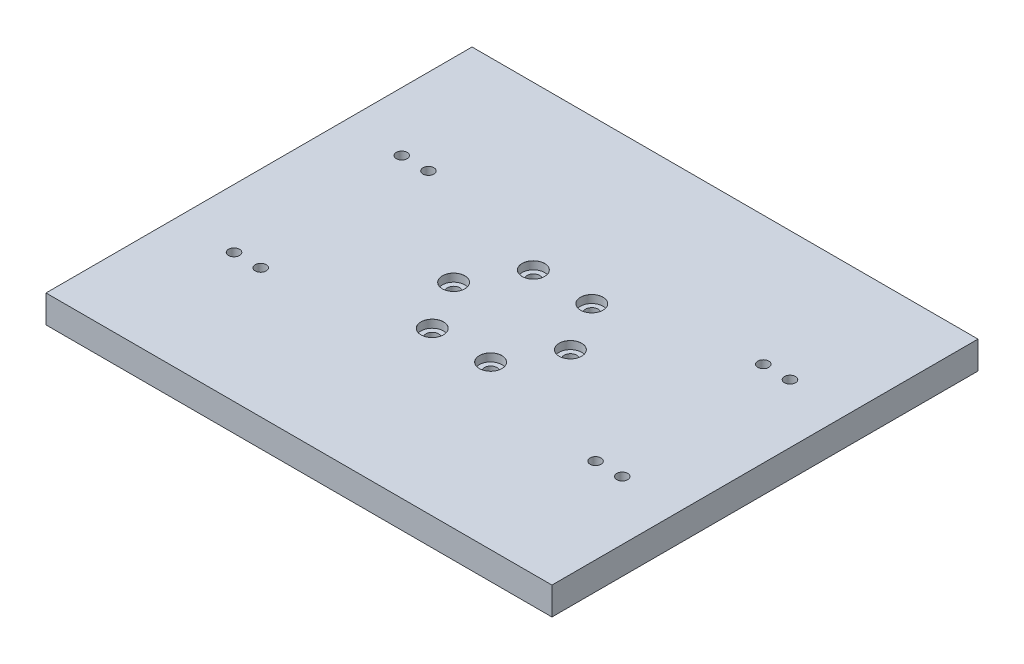
SolidWorks part; units mm, degrees
ref_plane "Front Plane" through (0, 0, 0) normal (0, 0, 1) x (1, 0, 0)
ref_plane "Top Plane" through (0, 0, 0) normal (0, 1, 0) x (1, 0, 0)
ref_plane "Right Plane" through (0, 0, 0) normal (1, 0, 0) x (0, 0, -1)
sketch "Sketch1" plane through (0, 0, 0) normal (0, 1, 0) x (1, 0, 0)
  line L1 (-241.3, -203.2) -> (241.3, -203.2)
  line L2 (-241.3, -203.2) -> (-241.3, 203.2)
  line L3 (-241.3, 203.2) -> (241.3, 203.2)
  line L4 (241.3, -203.2) -> (241.3, 203.2)
  line L5 (-241.3, -203.2) -> (241.3, 203.2) construction
  line L6 (-241.3, 203.2) -> (241.3, -203.2) construction
  point P0 (0, 0)
  dimension "D1" = 406.4
  dimension "D2" = 482.6
extrude "Boss-Extrude1" add sketch "Sketch1" along normal blind 26.416
sketch "Sketch3" plane through (0, 26.416, 0) normal (0, 1, 0) x (1, 0, 0)
  line L1 (-197.7873, -67.31) -> (-121.5873, -67.31) construction
  line L2 (-197.7873, -67.31) -> (-197.7873, -92.71) construction
  line L3 (-197.7873, -92.71) -> (-121.5873, -92.71) construction
  line L4 (-121.5873, -67.31) -> (-121.5873, -92.71) construction
  line L5 (-197.7873, -67.31) -> (-121.5873, -92.71) construction
  line L6 (-197.7873, -92.71) -> (-121.5873, -67.31) construction
  line L7 (-241.3, 203.2) -> (-241.3, -203.2) construction
  line L8 (0, 203.2) -> (0, -188.1619) construction
  line L9 (241.3, 203.2) -> (-241.3, 203.2) construction
  line L10 (-241.3, 0) -> (265.7597, 0) construction
  line L11 (-197.7873, 92.71) -> (-121.5873, 92.71) construction
  line L12 (-121.5873, 67.31) -> (-121.5873, 92.71) construction
  line L13 (-197.7873, 67.31) -> (-121.5873, 67.31) construction
  line L14 (-197.7873, 67.31) -> (-197.7873, 92.71) construction
  line L15 (197.7873, -92.71) -> (121.5873, -92.71) construction
  line L16 (121.5873, -67.31) -> (121.5873, -92.71) construction
  line L17 (197.7873, -67.31) -> (121.5873, -67.31) construction
  line L18 (197.7873, -67.31) -> (197.7873, -92.71) construction
  line L19 (197.7873, 67.31) -> (197.7873, 92.71) construction
  line L20 (197.7873, 67.31) -> (121.5873, 67.31) construction
  line L21 (121.5873, 67.31) -> (121.5873, 92.71) construction
  line L22 (197.7873, 92.71) -> (121.5873, 92.71) construction
  circle A0 centre (-185.1526, -80.01) radius 1.27
  circle A1 centre (-159.6873, -80.01) radius 1.27
  circle A2 centre (-185.1526, 80.01) radius 1.27
  circle A3 centre (-159.6873, 80.01) radius 1.27
  circle A4 centre (159.6873, -80.01) radius 1.27
  circle A5 centre (185.1526, -80.01) radius 1.27
  circle A6 centre (185.1526, 80.01) radius 1.27
  circle A7 centre (159.6873, 80.01) radius 1.27
  circle A15 centre (55.7, 0) radius 5.25
  circle A16 centre (27.85, -48.2376) radius 5.25
  circle A17 centre (-27.85, -48.2376) radius 5.25
  circle A18 centre (-55.7, 0) radius 5.25
  circle A19 centre (-27.85, 48.2376) radius 5.25
  circle A20 centre (27.85, 48.2376) radius 5.25
  point P0 (-159.6873, -80.01)
  point P59 (0, 0)
  dimension "D5" = 12.6347
  dimension "D6" = 25.4653
  dimension "D7" = 2.54
  dimension "D8" = 55.7
  dimension "D9" = 10.5
  dimension "D1" = 76.2
  dimension "D2" = 25.4
  dimension "D3" = 80.01
  dimension "D4" = 197.7873
extrude "Cut-Extrude2" cut sketch "Sketch3" against normal through all
hole_wizard "CBORE for M10 Hex Head Bolt1" positions "Sketch10" profile "Sketch11" counterbore size "M10" standard "ANSI Metric" end condition through all
sketch "Sketch10" plane through (0, 26.416, 0) normal (0, 1, 0) x (1, 0, 0)
  point P0 (27.85, 48.2376)
  point P3 (55.7, 0)
  point P6 (27.85, -48.2376)
  point P9 (-27.85, -48.2376)
  point P12 (-55.7, 0)
  point P15 (-27.85, 48.2376)
sketch "Sketch11" plane through (27.85, 26.416, -48.2376) normal (1, 0, 0) x (0, 0, 1)
  line L0 (0, 0) -> (0, 26.416)
  line L1 (0, 26.416) -> (6, 26.416)
  line L3 (6, 26.416) -> (6, 7.5)
  line L4 (10.74, 7.5) -> (6, 7.5)
  line L5 (10.74, 7.5) -> (10.74, 0.025)
  line L6 (10.74, 0.025) -> (10.765, 0)
  line L7 (10.765, 0) -> (0, 0)
  line L8 (-10.74, 0.025) -> (-10.765, 0) construction
  line L11 (0, -6.35) -> (0, 107.95) construction
  dimension "Thru Hole Dia." = 12
  dimension "Thru Hole Depth" = 26.416
  dimension "C'Bore Dia." = 21.48
  dimension "C'Bore Depth" = 7.5
  dimension "Near C'Sink Dia." = 21.53
  dimension "Near C'Sink Angle" = 90
hole_wizard "Tap Drill for M10 Helicoil1" positions "Sketch12" profile "Sketch13" hole size "M10x1.5" standard "ANSI Metric" end condition through all
sketch "Sketch12" plane through (0, 26.416, 0) normal (0, 1, 0) x (1, 0, 0)
  point P0 (-185.1526, -80.01)
  point P3 (-159.6873, -80.01)
  point P7 (-185.1526, 80.01)
  point P10 (-159.6873, 80.01)
  point P13 (185.1526, 80.01)
  point P16 (159.6873, 80.01)
  point P19 (185.1526, -80.01)
  point P22 (159.6873, -80.01)
sketch "Sketch13" plane through (-185.1526, 26.416, 80.01) normal (1, 0, 0) x (0, 0, 1)
  line L0 (0, 0) -> (0, 26.416)
  line L1 (0, 26.416) -> (5.25, 26.416)
  line L2 (5.25, 26.416) -> (5.25, 0)
  line L5 (5.25, 0) -> (0, 0)
  line L11 (0, -6.35) -> (0, 107.95) construction
  dimension "Thru Hole Dia." = 10.5
  dimension "Thru Hole Depth" = 26.416
